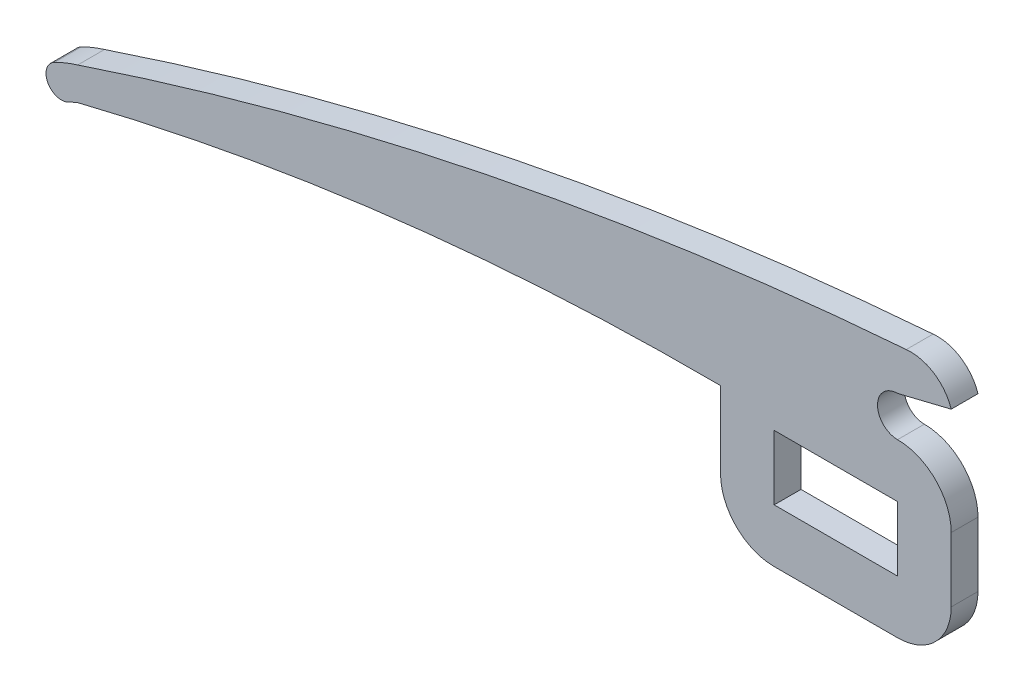
SolidWorks part; units mm, degrees
ref_plane "Front Plane" through (0, 0, 0) normal (0, 0, 1) x (1, 0, 0)
ref_plane "Top Plane" through (0, 0, 0) normal (0, 1, 0) x (1, 0, 0)
ref_plane "Right Plane" through (0, 0, 0) normal (1, 0, 0) x (0, 0, -1)
sketch "Sketch4" plane through (0, 0, 0) normal (0, 0, 1) x (1, 0, 0)
  line L0 (0, 0) -> (-23.0108, 0)
  line L1 (-23.0108, 0) -> (-23.0108, 12.0354)
  line L2 (-23.0108, 12.0354) -> (0, 12.0354)
  line L3 (0, 12.0354) -> (0, 0)
  line L4 (-23.0295, -9.9695) -> (0.0201, -9.9695)
  line L5 (-33.0178, 12.0354) -> (-33.0178, 0.0187)
  line L6 (-33.0178, 12.0354) -> (-33.0178, 14.2611)
  line L7 (10.0096, 12.0354) -> (10.0096, 0.02)
  line L9 (10.0096, 31.9659) -> (0.0023, 29.5135)
  arc A0 (10.0096, 0.02) -> (0.0201, -9.9695) centre (0.0201, 0.02) cw
  arc A1 (-23.0295, -9.9695) -> (-33.0178, 0.0187) centre (-23.0295, 0.0187) cw
  arc A2 (1.6315, 37.4137) -> (10.0096, 31.9659) centre (2.4547, 29.5135) cw
  arc A3 (0.0023, 22.0404) -> (10.0096, 12.0354) centre (0.0023, 12.0331) cw
  arc A5 (-152.9228, 0.0187) -> (-33.0178, 14.2611) centre (-36.4352, -468.8225) cw
  arc A6 (-152.9228, 6.1092) -> (-157.2654, 4.3613) centre (-144.8954, -20.1017) ccw
  arc A7 (-157.2654, 4.3613) -> (-154.6707, -0.7701) centre (-155.968, 1.7956) ccw
  arc A8 (-154.6707, -0.7701) -> (-152.9228, 0.0187) centre (-144.8882, -20.1161) cw
  arc A9 (0.0023, 29.5135) -> (0.0023, 22.0404) centre (0.0023, 25.777) ccw
  arc A10 (-152.9228, 6.1092) -> (1.6315, 37.4137) centre (50.6287, -601.6709) cw
  dimension "D1" = 23.0108
  dimension "D2" = 12.0354
  dimension "D3" = 122.9503
extrude "Boss-Extrude1" add sketch "Sketch4" along normal blind 5
move or copy body "Body-Move/Copy1" bodies to move or copy 102
